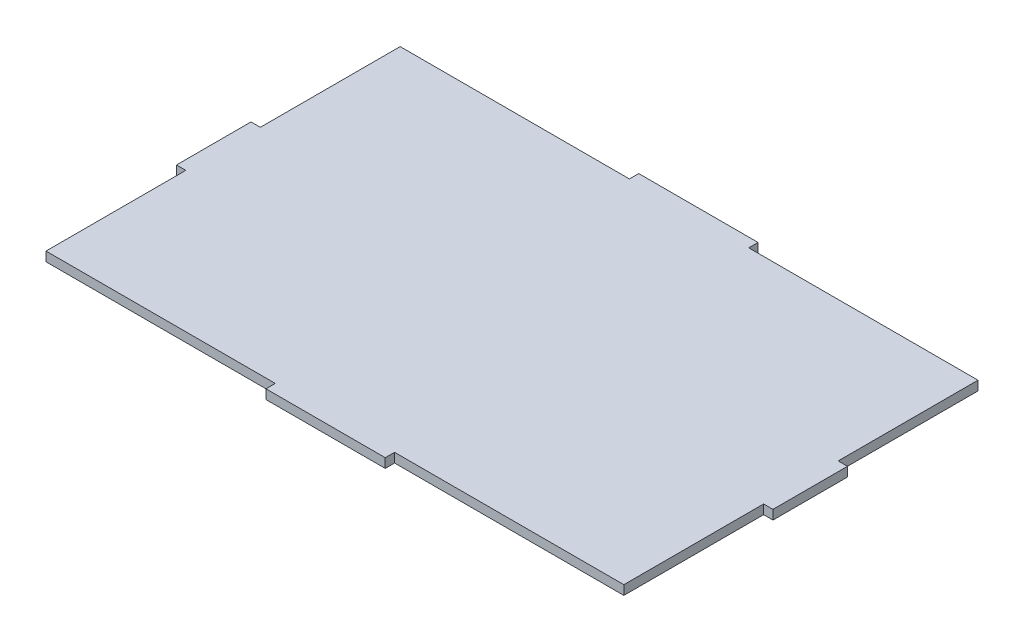
SolidWorks part; units mm, degrees
ref_plane "Front Plane" through (0, 0, 0) normal (0, 0, 1) x (1, 0, 0)
ref_plane "Top Plane" through (0, 0, 0) normal (0, 1, 0) x (1, 0, 0)
ref_plane "Right Plane" through (0, 0, 0) normal (1, 0, 0) x (0, 0, -1)
sketch "Sketch1" plane through (0, 0, 0) normal (0, 1, 0) x (1, 0, 0)
  line L1 (-101.6, -63.5) -> (101.6, -63.5)
  line L2 (-101.6, -63.5) -> (-101.6, 63.5)
  line L3 (-101.6, 63.5) -> (101.6, 63.5)
  line L4 (101.6, -63.5) -> (101.6, 63.5)
  line L5 (-101.6, -63.5) -> (101.6, 63.5) construction
  line L6 (-101.6, 63.5) -> (101.6, -63.5) construction
  point P0 (0, 0)
  dimension "D1" = 127
  dimension "D2" = 203.2
extrude "Boss-Extrude1" add sketch "Sketch1" along normal blind 3.175
sketch "Sketch2" plane through (0, 3.175, 0) normal (0, 1, 0) x (1, 0, 0)
  line L0 (-101.6, 63.5) -> (-101.6, -63.5) construction
  line L1 (-104.775, -12.7) -> (-98.425, -12.7) construction
  line L2 (-104.775, -12.7) -> (-104.775, 12.7) construction
  line L3 (-104.775, 12.7) -> (-98.425, 12.7) construction
  line L4 (-98.425, -12.7) -> (-98.425, 12.7) construction
  line L5 (-104.775, -12.7) -> (-98.425, 12.7) construction
  line L6 (-104.775, 12.7) -> (-98.425, -12.7) construction
  line L7 (101.6, -63.5) -> (101.6, 63.5) construction
  line L8 (98.425, -12.7) -> (104.775, -12.7) construction
  line L9 (98.425, -12.7) -> (98.425, 12.7) construction
  line L10 (98.425, 12.7) -> (104.775, 12.7) construction
  line L11 (104.775, -12.7) -> (104.775, 12.7) construction
  line L12 (98.425, -12.7) -> (104.775, 12.7) construction
  line L13 (98.425, 12.7) -> (104.775, -12.7) construction
  line L14 (-101.6, -63.5) -> (101.6, -63.5) construction
  line L15 (-20.32, -66.675) -> (20.32, -66.675) construction
  line L16 (-20.32, -66.675) -> (-20.32, -60.325) construction
  line L17 (-20.32, -60.325) -> (20.32, -60.325) construction
  line L18 (20.32, -66.675) -> (20.32, -60.325) construction
  line L19 (-20.32, -66.675) -> (20.32, -60.325) construction
  line L20 (-20.32, -60.325) -> (20.32, -66.675) construction
  line L21 (-101.6, 12.7) -> (-101.6, 63.5)
  line L22 (-98.425, 60.325) -> (98.425, 60.325) construction
  line L23 (-98.425, 60.325) -> (-98.425, -60.325) construction
  line L24 (-98.425, -60.325) -> (98.425, -60.325) construction
  line L25 (98.425, 60.325) -> (98.425, -60.325) construction
  line L26 (-98.425, 60.325) -> (98.425, -60.325) construction
  line L27 (-98.425, -60.325) -> (98.425, 60.325) construction
  line L28 (-101.6, 63.5) -> (101.6, 63.5)
  line L29 (101.6, 63.5) -> (101.6, 12.7)
  line L30 (101.6, 12.7) -> (98.425, 12.7)
  line L31 (98.425, 12.7) -> (98.425, 60.325)
  line L32 (98.425, 60.325) -> (-98.425, 60.325)
  line L33 (-98.425, 60.325) -> (-98.425, 12.7)
  line L34 (-98.425, 12.7) -> (-101.6, 12.7)
  line L35 (-98.425, -12.7) -> (-98.425, -60.325)
  line L36 (-98.425, -60.325) -> (-20.32, -60.325)
  line L37 (-20.32, -60.325) -> (-20.32, -63.5)
  line L38 (-20.32, -63.5) -> (-101.6, -63.5)
  line L39 (-101.6, -63.5) -> (-101.6, -12.7)
  line L40 (-101.6, -12.7) -> (-98.425, -12.7)
  line L41 (20.32, -60.325) -> (20.32, -63.5)
  line L42 (20.32, -63.5) -> (101.6, -63.5)
  line L43 (101.6, -63.5) -> (101.6, -12.7)
  line L44 (101.6, -12.7) -> (98.425, -12.7)
  line L45 (98.425, -12.7) -> (98.425, -60.325)
  line L46 (98.425, -60.325) -> (20.32, -60.325)
  point P0 (-101.6, 0)
  point P7 (101.6, 0)
  point P14 (0, -63.5)
  point P22 (0, 0)
  dimension "D1" = 25.4
  dimension "D2" = 6.35
  dimension "D3" = 6.35
  dimension "D4" = 40.64
  dimension "D5" = 6.35
sketch "Sketch3" plane through (0, 3.175, 0) normal (0, 1, 0) x (1, 0, 0)
  line L0 (-101.6, 63.5) -> (101.6, 63.5) construction
  line L1 (-20.32, 66.675) -> (20.32, 66.675) construction
  line L2 (-20.32, 66.675) -> (-20.32, 60.325) construction
  line L3 (-20.32, 60.325) -> (20.32, 60.325) construction
  line L4 (20.32, 66.675) -> (20.32, 60.325) construction
  line L5 (-20.32, 66.675) -> (20.32, 60.325) construction
  line L6 (-20.32, 60.325) -> (20.32, 66.675) construction
  line L8 (-98.425, 12.7) -> (-101.6, 12.7)
  line L9 (-101.6, 12.7) -> (-101.6, 63.5)
  line L10 (-101.6, 63.5) -> (-20.32, 63.5)
  line L11 (-20.32, 63.5) -> (-20.32, 60.325)
  line L12 (-20.32, 60.325) -> (-98.425, 60.325)
  line L13 (-98.425, 60.325) -> (-98.425, 12.7)
  line L14 (20.32, 60.325) -> (98.425, 60.325)
  line L15 (98.425, 60.325) -> (98.425, 12.7)
  line L16 (98.425, 12.7) -> (101.6, 12.7)
  line L17 (101.6, 12.7) -> (101.6, 63.5)
  line L18 (101.6, 63.5) -> (20.32, 63.5)
  line L19 (20.32, 63.5) -> (20.32, 60.325)
  line L20 (-101.6, -12.7) -> (-101.6, -65.5134)
  line L21 (-101.6, -65.5134) -> (-20.32, -63.5)
  line L22 (-20.32, -63.5) -> (-20.32, -60.325)
  line L23 (-20.32, -60.325) -> (-98.425, -60.325)
  line L24 (-98.425, -60.325) -> (-98.425, -12.7)
  line L25 (-98.425, -12.7) -> (-101.6, -12.7)
  line L26 (20.32, -60.325) -> (20.32, -63.5)
  line L27 (20.32, -63.5) -> (101.6, -63.5)
  line L28 (101.6, -63.5) -> (101.6, -12.7)
  line L29 (101.6, -12.7) -> (98.425, -12.7)
  line L30 (98.425, -12.7) -> (98.425, -60.325)
  line L31 (98.425, -60.325) -> (20.32, -60.325)
  point P0 (0, 63.5)
  dimension "D1" = 6.35
extrude "Cut-Extrude1" cut sketch "Sketch3" against normal blind 3.175
